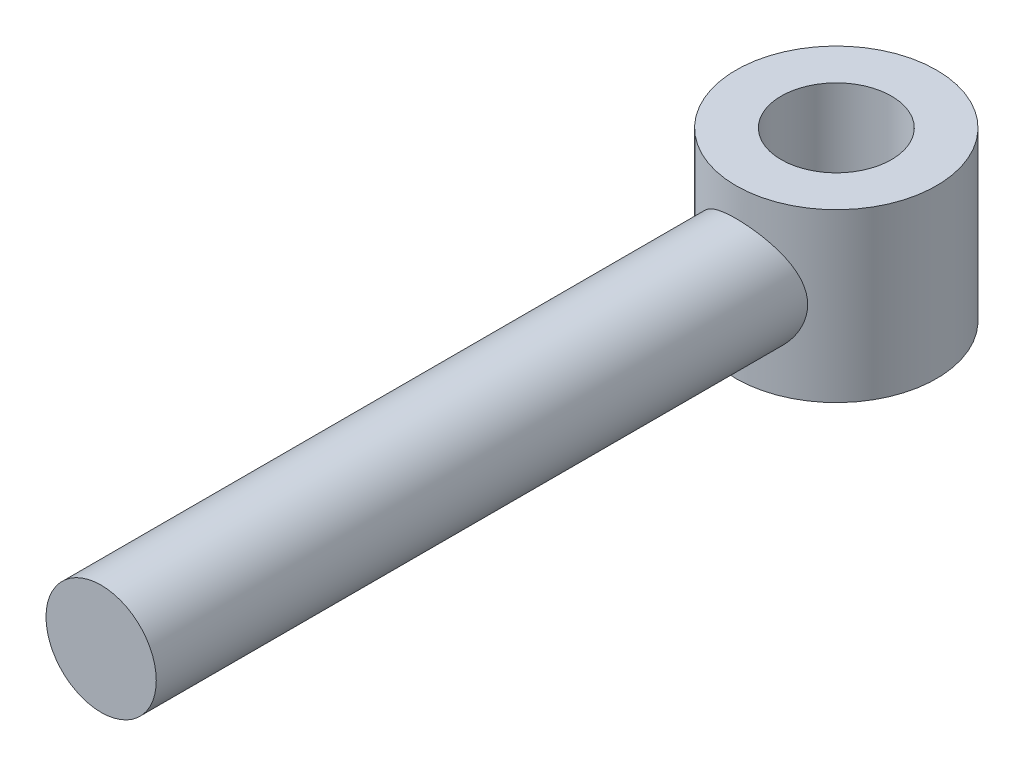
SolidWorks part; units mm, degrees
ref_plane "Přední rovina" through (0, 0, 0) normal (0, 0, 1) x (1, 0, 0)
ref_plane "Horní rovina" through (0, 0, 0) normal (0, 1, 0) x (1, 0, 0)
ref_plane "Pravá rovina" through (0, 0, 0) normal (1, 0, 0) x (0, 0, -1)
sketch "Skica1" plane through (0, 0, 0) normal (0, 0, 1) x (1, 0, 0)
  circle A0 centre (0, 0) radius 1.65
  dimension "D1" = 3.3
extrude "Přidat vysunutím1" add sketch "Skica1" along normal blind 20
sketch "Skica2" plane through (0, 0, 0) normal (0, 1, 0) x (1, 0, 0)
  circle A0 centre (0, 2) radius 3
  dimension "D1" = 6
  dimension "D2" = 2
extrude "Přidat vysunutím2" add sketch "Skica2" along normal mid plane 5
sketch "Skica4" plane through (0, 2.5, 0) normal (0, 1, 0) x (1, 0, 0)
  circle A0 centre (0, 2.0011) radius 1.65
  dimension "D1" = 3.3
extrude "Odebrat vysunutím1" cut sketch "Skica4" against normal blind 5
